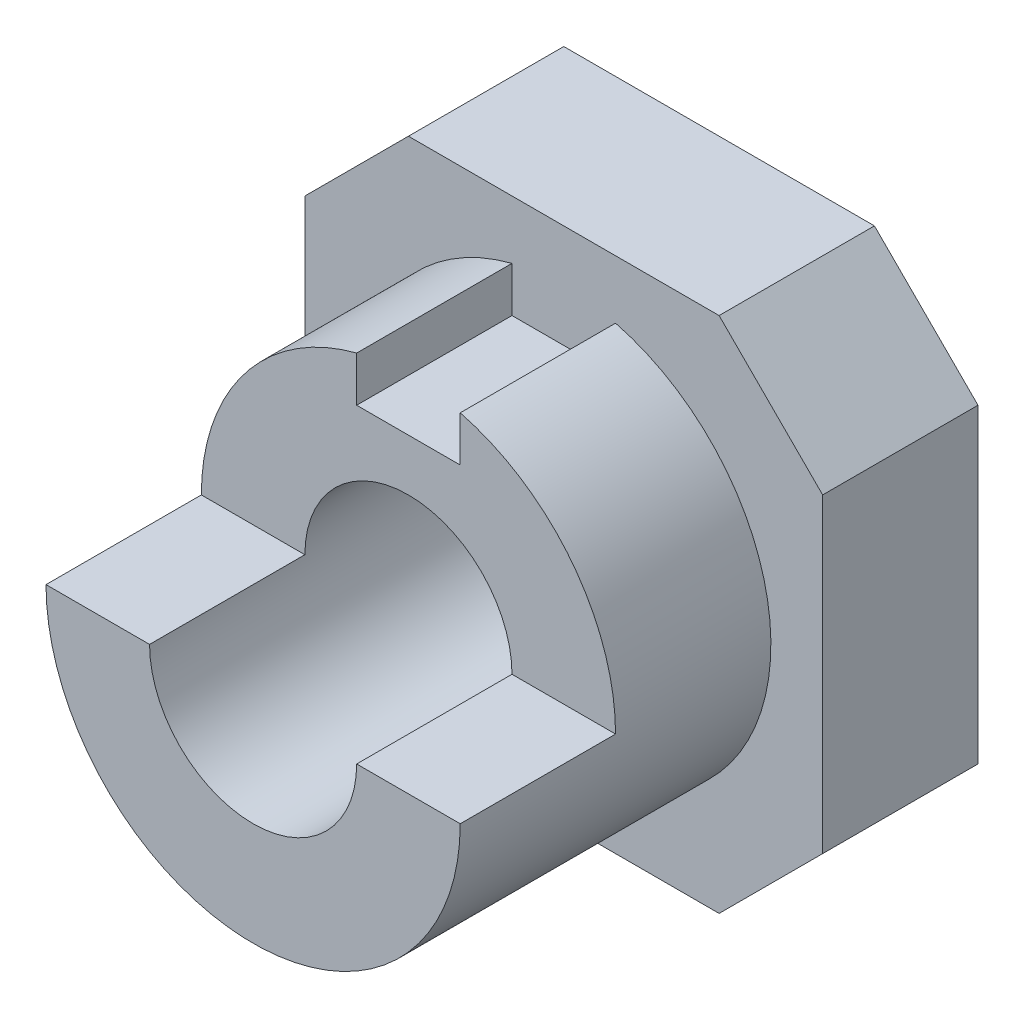
SolidWorks part; units mm, degrees
ref_plane "Front" through (0, 0, 0) normal (0, 0, 1) x (1, 0, 0)
ref_plane "Top" through (0, 0, 0) normal (0, 1, 0) x (1, 0, 0)
ref_plane "Right" through (0, 0, 0) normal (1, 0, 0) x (0, 0, -1)
sketch "Sketch2" plane through (0, 0, 0) normal (0, 0, 1) x (1, 0, 0)
  line L0 (-5, 3) -> (-3, 5)
  line L1 (-3, -5) -> (3, -5)
  line L2 (-5, -3) -> (-5, 3)
  line L3 (-3, 5) -> (3, 5)
  line L4 (5, -3) -> (5, 3)
  line L5 (-5, -5) -> (5, 5) construction
  line L6 (-5, 5) -> (5, -5) construction
  line L7 (3, 5) -> (5, 3)
  line L8 (3, -5) -> (5, -3)
  line L9 (-5, -3) -> (-3, -5)
  circle A0 centre (0, 0) radius 2
  point P0 (0, 0)
  dimension "D3" = 4
  dimension "D1" = 10
  dimension "D2" = 10
extrude "Boss-Extrude1" add sketch "Sketch2" along normal blind 3
sketch "Sketch3" plane through (0, 0, 3) normal (0, 0, 1) x (1, 0, 0)
  line L0 (1, 3) -> (-1, 3)
  line L1 (-1, 3) -> (-1, 3.873)
  line L2 (1, 3) -> (1, 3.873)
  circle A0 centre (0, 0) radius 2
  arc A1 (-1, 3.873) -> (1, 3.873) centre (0, 0) ccw
  dimension "D1" = 8
  dimension "D2" = 3
  dimension "D3" = 2
  dimension "D4" = 1
extrude "Boss-Extrude2" add sketch "Sketch3" along normal blind 6
sketch "Sketch4" plane through (0, 0, 9) normal (0, 0, 1) x (1, 0, 0)
  line L1 (-4, 0) -> (4, 0)
  line L2 (-4, 0) -> (-4, 4.6034)
  line L3 (-4, 4.6034) -> (4, 4.6034)
  line L4 (4, 0) -> (4, 4.6034)
  arc A0 (-1, 3.873) -> (1, 3.873) centre (0, 0) ccw construction
  arc A1 (-1, 3.873) -> (1, 3.873) centre (0, 0) ccw construction
extrude "Cut-Extrude1" cut sketch "Sketch4" against normal blind 3
